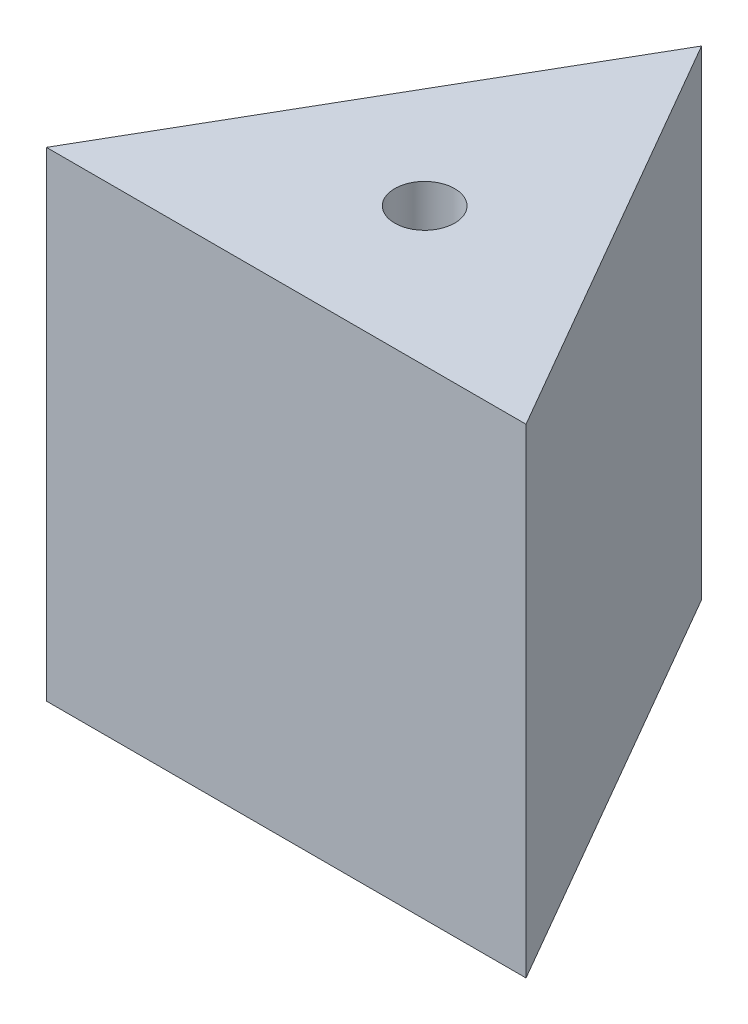
SolidWorks part; units mm, degrees
ref_plane "Front Plane" through (0, 0, 0) normal (0, 0, 1) x (1, 0, 0)
ref_plane "Top Plane" through (0, 0, 0) normal (0, 1, 0) x (1, 0, 0)
ref_plane "Right Plane" through (0, 0, 0) normal (1, 0, 0) x (0, 0, -1)
sketch "Sketch1" plane through (0, 0, 0) normal (0, 1, 0) x (1, 0, 0)
  line L0 (0, 0) -> (-152.4, -263.9645)
  line L1 (-152.4, -263.9645) -> (152.4, -263.9645)
  line L2 (152.4, -263.9645) -> (0, 0)
extrude "Boss-Extrude1" add sketch "Sketch1" along normal blind 304.8
sketch "Sketch2" plane through (0, 304.8, 0) normal (0, 1, 0) x (1, 0, 0)
  line L0 (0, 0) -> (0, -263.9645) construction
  line L1 (-152.4, -263.9645) -> (152.4, -263.9645) construction
  line L2 (-152.4, -263.9645) -> (76.2, -131.9823) construction
  line L3 (152.4, -263.9645) -> (0, 0) construction
  circle A0 centre (0, -175.9764) radius 19.05
extrude "Cut-Extrude1" cut sketch "Sketch2" against normal through all
sketch "Sketch3" plane through (0, 304.8, 0) normal (0, 1, 0) x (1, 0, 0)
  line L0 (0, 0) -> (0, -156.9264)
  line L1 (0, -195.0264) -> (0, -263.9645)
  line L2 (-152.4, -263.9645) -> (152.4, -263.9645) construction
  circle A0 centre (0, -175.9764) radius 19.05 construction
